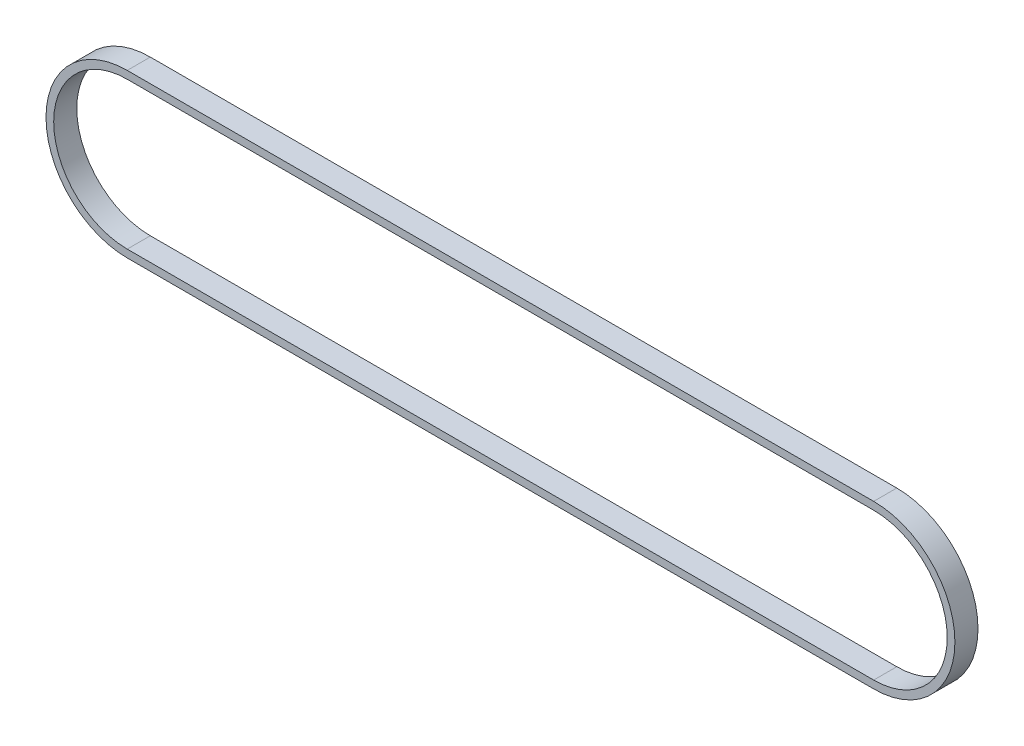
SolidWorks part; units mm, degrees
ref_plane "Front Plane" through (0, 0, 0) normal (0, 0, 1) x (1, 0, 0)
ref_plane "Top Plane" through (0, 0, 0) normal (0, 1, 0) x (1, 0, 0)
ref_plane "Right Plane" through (0, 0, 0) normal (1, 0, 0) x (0, 0, -1)
sketch "Sketch1" plane through (0, 0, 0) normal (0, 0, 1) x (1, 0, 0)
  line L0 (0, 19.11) -> (194, 19.11)
  line L1 (194, -19.11) -> (0, -19.11)
  line L2 (194, -21.11) -> (0, -21.11)
  line L3 (0, 21.11) -> (194, 21.11)
  arc A0 (0, 19.11) -> (0, -19.11) centre (0, 0) ccw
  arc A1 (194, -19.11) -> (194, 19.11) centre (194, 0) ccw
  arc A2 (0, 21.11) -> (0, -21.11) centre (0, 0) ccw
  arc A3 (194, -21.11) -> (194, 21.11) centre (194, 0) ccw
  dimension "D1" = 194
  dimension "D3" = 19.11
  dimension "D2" = 2
extrude "Boss-Extrude1" add sketch "Sketch1" along normal blind 6
